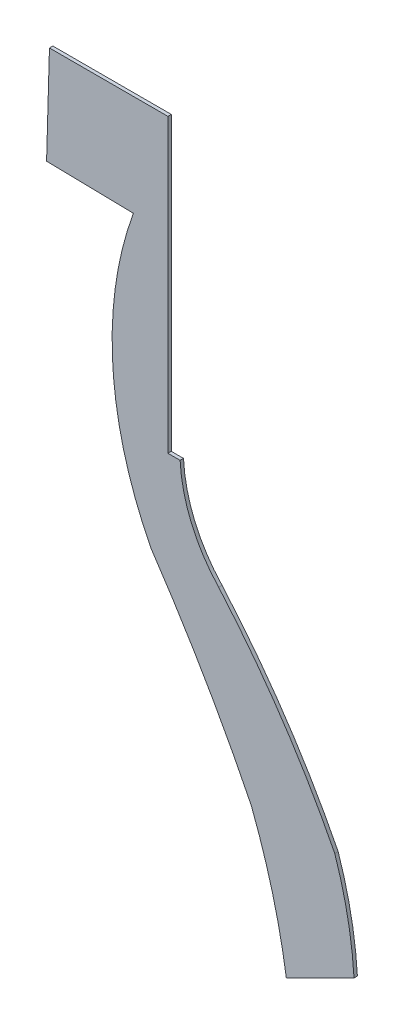
SolidWorks part; units mm, degrees
ref_plane "Alzado" through (0, 0, 0) normal (0, 0, 1) x (1, 0, 0)
ref_plane "Planta" through (0, 0, 0) normal (0, 1, 0) x (1, 0, 0)
ref_plane "Vista lateral" through (0, 0, 0) normal (1, 0, 0) x (0, 0, -1)
sketch "Model" plane through (0, 0, 0) normal (0, 0, 1) x (1, 0, 0)
  line L0 (12.6983, 13.8026) -> (15.2636, 13.7509)
  line L1 (12.7828, 16.7418) -> (16.2841, 16.7418)
  line L2 (16.2841, 8.1198) -> (16.2841, 16.7418)
  line L3 (16.6437, 8.1198) -> (16.2841, 8.1198)
  line L4 (19.7828, -3.5582) -> (21.7828, -2.5582)
  line L5 (12.7828, 16.7418) -> (12.6983, 13.8026)
  arc A0 (16.6437, 8.1198) -> (17.7828, 5.4418) centre (20.8832, 8.3419) ccw
  arc A1 (21.214, 0.3418) -> (17.7828, 5.4418) centre (-1.0379, -10.9245) ccw
  arc A2 (19.7828, -3.5582) -> (18.7454, 0.3418) centre (1.7513, -6.2669) ccw
  arc A3 (21.7828, -2.5582) -> (21.214, 0.3418) centre (10.6731, -3.2317) ccw
  arc A4 (18.7454, 0.3418) -> (15.7828, 5.4418) centre (-19.7541, -18.6117) ccw
  arc A5 (15.2636, 13.7509) -> (15.7828, 5.4418) centre (25.0285, 10.1903) ccw
extrude "Saliente-Extruir1" add sketch "Model" along normal blind 0.1
